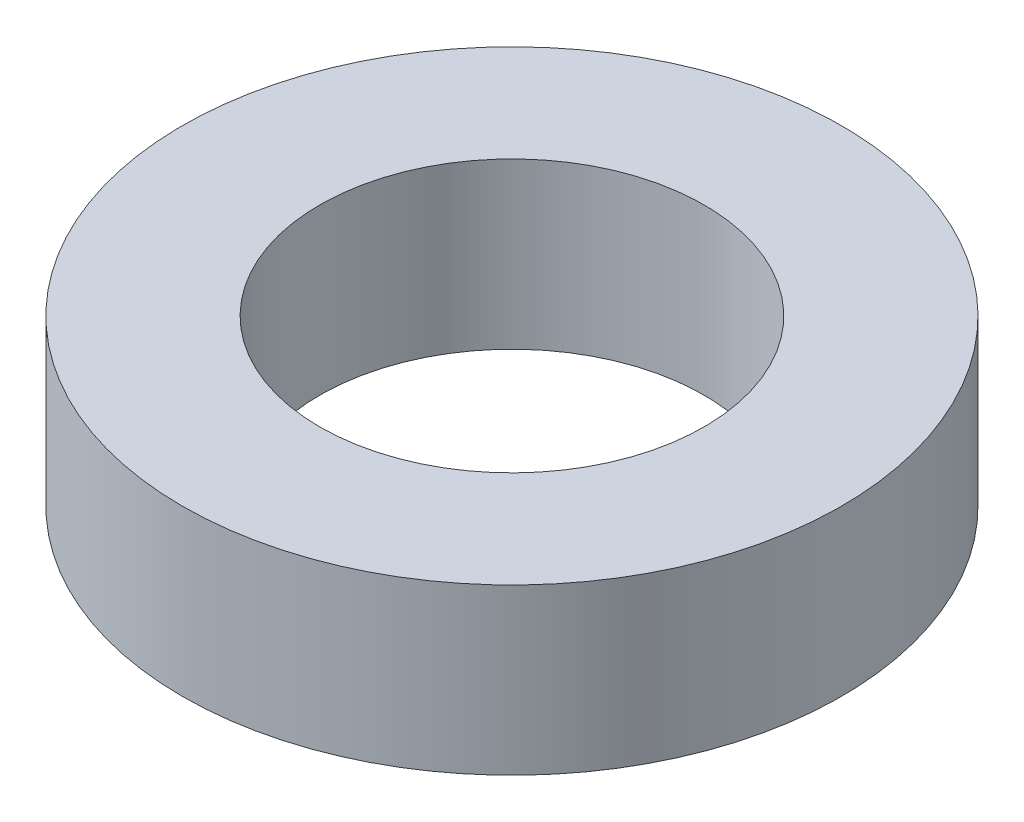
SolidWorks part; units mm, degrees
ref_plane "Front Plane" through (0, 0, 0) normal (0, 0, 1) x (1, 0, 0)
ref_plane "Top Plane" through (0, 0, 0) normal (0, 1, 0) x (1, 0, 0)
ref_plane "Right Plane" through (0, 0, 0) normal (1, 0, 0) x (0, 0, -1)
sketch "Sketch1" plane through (0, 0, 0) normal (0, 1, 0) x (1, 0, 0)
  circle A0 centre (0, 0) radius 1.75
  circle A1 centre (0, 0) radius 3
  dimension "D1" = 3.5
  dimension "D2" = 6
extrude "Boss-Extrude1" add sketch "Sketch1" along normal blind 1.5
